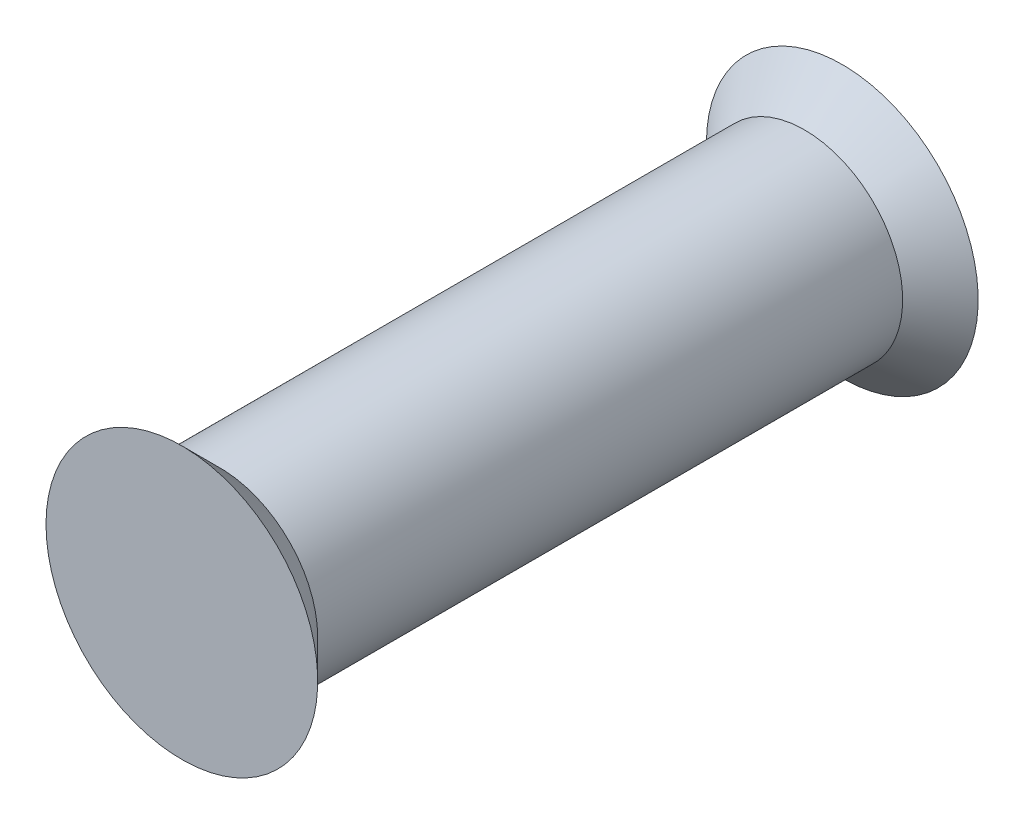
SolidWorks part; units mm, degrees
ref_plane "Front Plane" through (0, 0, 0) normal (0, 0, 1) x (1, 0, 0)
ref_plane "Top Plane" through (0, 0, 0) normal (0, 1, 0) x (1, 0, 0)
ref_plane "Right Plane" through (0, 0, 0) normal (1, 0, 0) x (0, 0, -1)
sketch "Sketch1" plane through (0, 0, 0) normal (0, 1, 0) x (1, 0, 0)
  line L0 (0, 13.6595) -> (0, -11.9383) construction
  line L1 (-11.5852, 0) -> (15.9104, 0) construction
  line L2 (0, 8.75) -> (-2.6, 8.75)
  line L3 (-2.6, 8.75) -> (-2.6, -8.75)
  line L4 (-2.6, -8.75) -> (0, -8.75)
  line L5 (0, -8.75) -> (0, 8.75)
  dimension "D1" = 5.2
  dimension "D2" = 17.5
revolve "Revolve1" add sketch "Sketch1" angle 360 about L0
sketch "Sketch2" plane through (0, 0, 0) normal (0, 1, 0) x (1, 0, 0)
  line L0 (-2.6, -7.75) -> (-3.6, -8.75)
  line L1 (-2.6, 8.75) -> (-2.6, -8.75) construction
  line L2 (-3.6, -8.75) -> (-2.6, -8.75)
  line L3 (-2.6, -8.75) -> (2.6, -8.75) construction
  line L4 (-2.6, -8.75) -> (-2.6, -7.75)
  line L5 (0, 14.7228) -> (0, -17.4222) construction
  dimension "D1" = 1
revolve "Revolve2" add sketch "Sketch2" angle 360 about L5
mirror "Mirror1" about plane through (0, 0, 0) normal (0, 0, 1) of "Revolve2"
